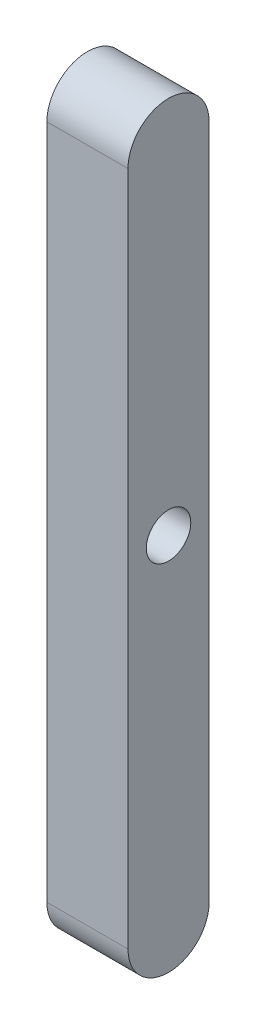
SolidWorks part; units mm, degrees
ref_plane "前视基准面" through (0, 0, 0) normal (0, 0, 1) x (1, 0, 0)
ref_plane "上视基准面" through (0, 0, 0) normal (0, 1, 0) x (1, 0, 0)
ref_plane "右视基准面" through (0, 0, 0) normal (1, 0, 0) x (0, 0, -1)
sketch "草图1" plane through (0, 0, 0) normal (1, 0, 0) x (0, 0, -1)
  line L0 (0, -25) -> (0, 25) construction
  line L1 (-3, -25) -> (-3, 25)
  line L2 (3, -25) -> (3, 25)
  arc A0 (-3, -25) -> (3, -25) centre (0, -25) ccw
  arc A1 (3, 25) -> (-3, 25) centre (0, 25) ccw
  circle A2 centre (0, 0) radius 1.6447
  point P2 (0, 0)
  dimension "D2" = 3
  dimension "D1" = 50
extrude "凸台-拉伸1" add sketch "草图1" along normal blind 6
